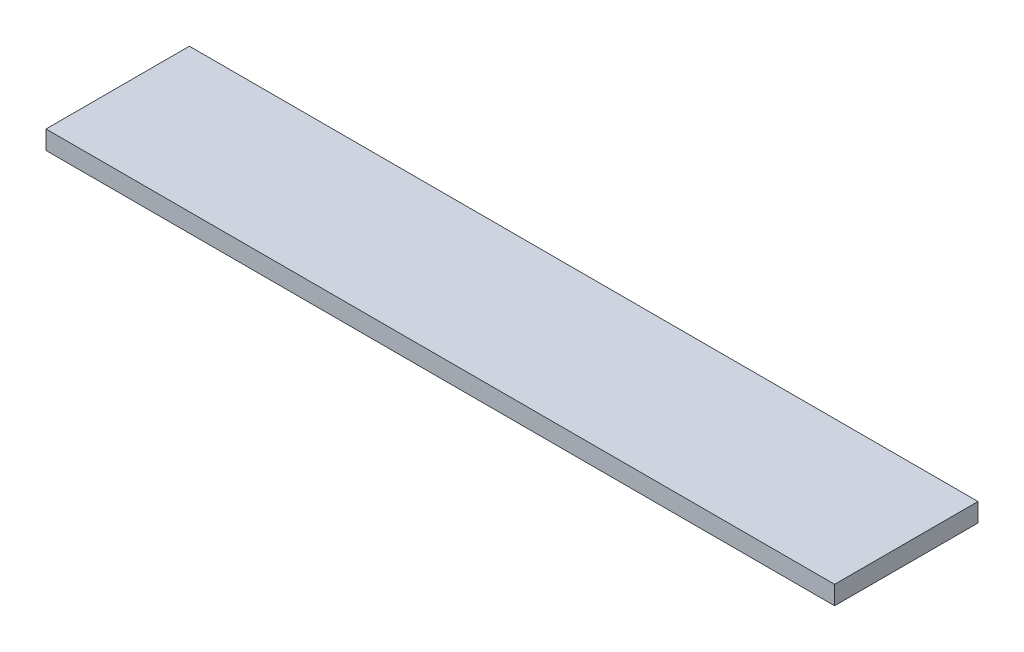
SolidWorks part; units mm, degrees
ref_plane "Front Plane" through (0, 0, 0) normal (0, 0, 1) x (1, 0, 0)
ref_plane "Top Plane" through (0, 0, 0) normal (0, 1, 0) x (1, 0, 0)
ref_plane "Right Plane" through (0, 0, 0) normal (1, 0, 0) x (0, 0, -1)
sketch "Sketch1" plane through (0, 0, 0) normal (0, 1, 0) x (1, 0, 0)
  line L1 (-34.925, -6.35) -> (34.925, -6.35)
  line L2 (-34.925, -6.35) -> (-34.925, 6.35)
  line L3 (-34.925, 6.35) -> (34.925, 6.35)
  line L4 (34.925, -6.35) -> (34.925, 6.35)
  line L5 (-34.925, -6.35) -> (34.925, 6.35) construction
  line L6 (-34.925, 6.35) -> (34.925, -6.35) construction
  point P0 (0, 0)
  dimension "D1" = 12.7
  dimension "D2" = 69.85
extrude "Boss-Extrude1" add sketch "Sketch1" along normal blind 1.651
equation "\"D1@Sketch1\"=0.5in"
